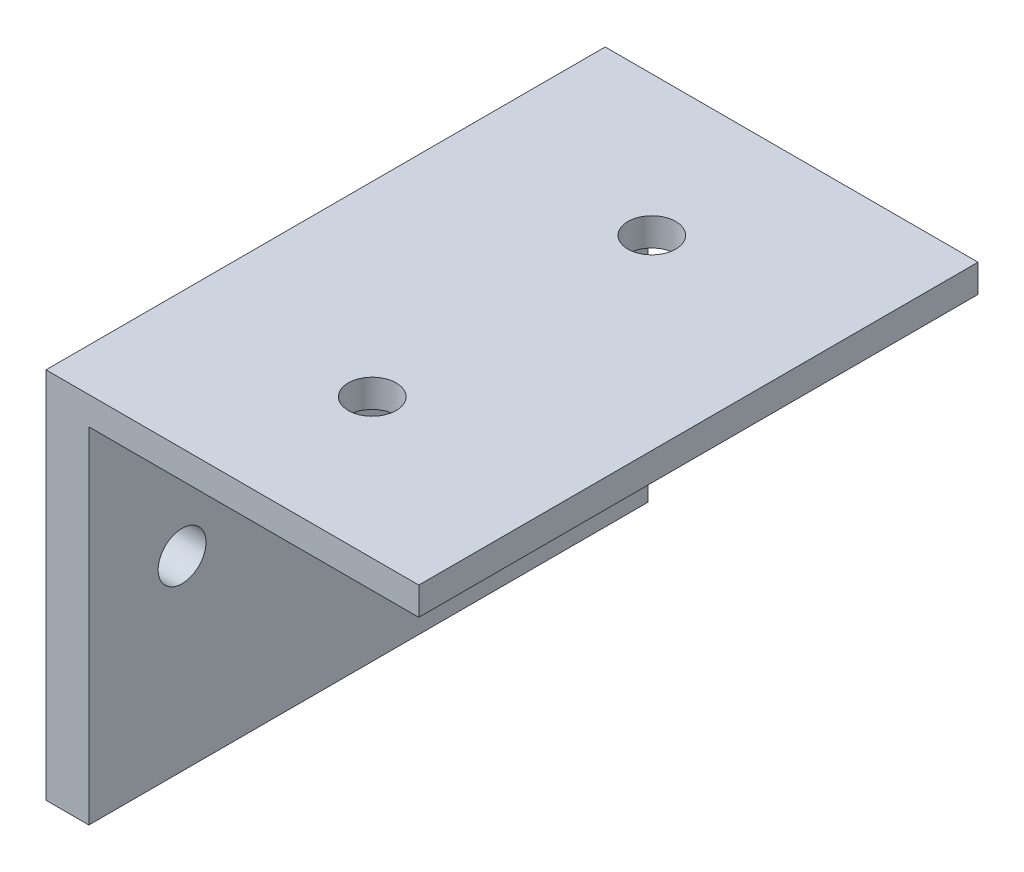
SolidWorks part; units mm, degrees
ref_plane "Front Plane" through (0, 0, 0) normal (0, 0, 1) x (1, 0, 0)
ref_plane "Top Plane" through (0, 0, 0) normal (0, 1, 0) x (1, 0, 0)
ref_plane "Right Plane" through (0, 0, 0) normal (1, 0, 0) x (0, 0, -1)
sketch "Sketch1" plane through (0, 0, 0) normal (0, 0, 1) x (1, 0, 0)
  line L0 (0, 0) -> (0, 50.8)
  line L1 (0, 50.8) -> (50.8, 50.8)
  line L2 (50.8, 50.8) -> (50.8, 46.99)
  line L3 (0, 0) -> (5.842, 0)
  line L4 (5.842, 0) -> (5.842, 46.99)
  line L5 (5.842, 46.99) -> (50.8, 46.99)
  dimension "D1" = 3.81
  dimension "D2" = 5.842
  dimension "D3" = 50.8
  dimension "D4" = 50.8
extrude "Boss-Extrude1" add sketch "Sketch1" along normal blind 76.2
sketch "Sketch2" plane through (0, 0, 0) normal (-1, 0, 0) x (0, 0, 1)
  line L0 (38.1, 50.8) -> (38.1, 0) construction
  line L1 (76.2, 50.8) -> (0, 50.8) construction
  line L2 (76.2, 0) -> (0, 0) construction
  line L3 (12.7, 25.4) -> (63.5, 25.4)
  point P9 (38.1, 25.4)
  dimension "D1" = 25.4
sketch "Sketch3" plane through (0, 50.8, 0) normal (0, 1, 0) x (1, 0, 0)
  line L0 (0, -38.1) -> (50.8, -38.1) construction
  line L1 (50.8, -76.2) -> (50.8, 0) construction
  line L2 (25.4, -19.05) -> (25.4, -57.15)
  line L3 (50.8, 0) -> (0, 0) construction
  point P10 (25.4, -38.1)
  dimension "D1" = 19.05
hole_wizard "F (0.257) Diameter Hole1" positions "3DSketch1" profile "Sketch4" hole size "F" standard "ANSI Inch" end condition up to next
sketch3d "3DSketch1"
  point P0 (0, 25.4, 12.7)
  point P3 (0, 25.4, 63.5)
  point P6 (25.4, 50.8, 19.05)
  point P9 (25.4, 50.8, 57.15)
sketch "Sketch4" plane through (0, 25.4, 12.7) normal (0, 1, 0) x (0, 0, 1)
  line L0 (0, 0) -> (0, 5.842)
  line L1 (0, 5.842) -> (3.2639, 5.842)
  line L2 (3.2639, 5.842) -> (3.2639, 0)
  line L5 (3.2639, 0) -> (0, 0)
  line L11 (0, -6.35) -> (0, 107.95) construction
  dimension "Thru Hole Dia." = 6.5278
  dimension "Thru Hole Depth" = 5.842
